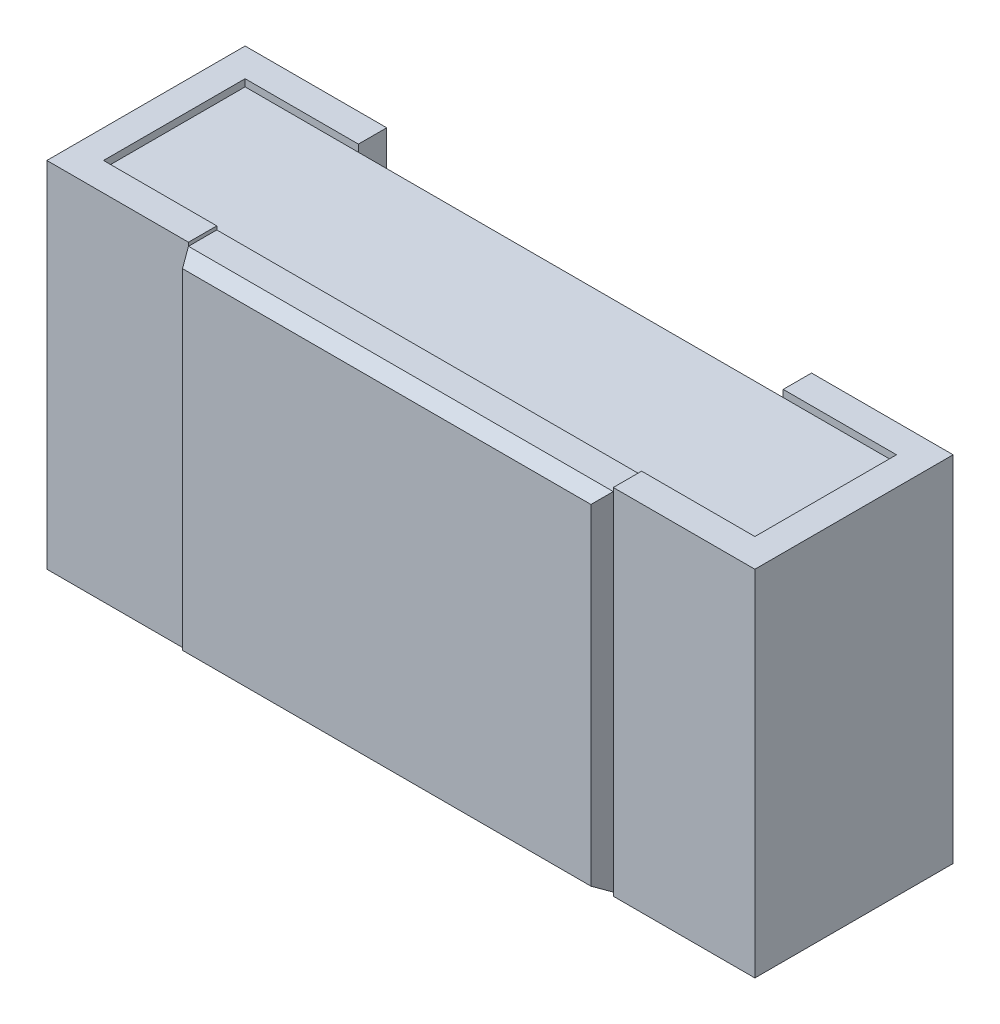
SolidWorks part; units mm, degrees
ref_plane "Спереди" through (0, 0, 0) normal (0, 0, 1) x (1, 0, 0)
ref_plane "Сверху" through (0, 0, 0) normal (0, 1, 0) x (1, 0, 0)
ref_plane "Справа" through (0, 0, 0) normal (1, 0, 0) x (0, 0, -1)
sketch "Эскиз2" plane through (0, 0, 0) normal (0, 0, 1) x (1, 0, 0)
  line L1 (-0.46, 0.24) -> (0.46, 0.24)
  line L2 (-0.46, 0.24) -> (-0.46, -0.24)
  line L3 (-0.46, -0.24) -> (0.46, -0.24)
  line L4 (0.46, 0.24) -> (0.46, -0.24)
  point P0 (0, 0)
extrude "Вытянуть2" add sketch "Эскиз2" along normal blind 0.2 from offset 0.04
sketch "Эскиз4" plane through (0, 0, 0) normal (0, 1, 0) x (1, 0, 0)
  line L0 (-0.5, 0) -> (-0.3, 0)
  line L1 (-0.46, -0.04) -> (-0.3, -0.04)
  line L2 (-0.5, 0) -> (-0.5, -0.28)
  line L3 (-0.3, 0) -> (-0.3, -0.04)
  line L4 (-0.46, -0.04) -> (-0.46, -0.24)
  line L5 (-0.5, -0.28) -> (-0.3, -0.28)
  line L6 (-0.3, -0.28) -> (-0.3, -0.24)
  line L7 (-0.3, -0.24) -> (-0.46, -0.24)
  line L8 (0, -0.3) -> (0, -0.2) construction
  line L9 (0.3, -0.24) -> (0.46, -0.24)
  line L10 (0.3, -0.28) -> (0.3, -0.24)
  line L11 (0.5, -0.28) -> (0.3, -0.28)
  line L12 (0.46, -0.04) -> (0.46, -0.24)
  line L13 (0.3, 0) -> (0.3, -0.04)
  line L14 (0.5, 0) -> (0.5, -0.28)
  line L15 (0.46, -0.04) -> (0.3, -0.04)
  line L16 (0.5, 0) -> (0.3, 0)
extrude "Вытянуть4" add sketch "Эскиз4" along normal blind 0.25 and the other way blind 0.25
sketch "Эскиз6" plane through (0, 0, 0) normal (0, 0, 1) x (1, 0, 0)
  line L1 (-0.3, 0.245) -> (0.3, 0.245)
  line L2 (-0.3, 0.245) -> (-0.3, -0.245)
  line L3 (-0.3, -0.245) -> (0.3, -0.245)
  line L4 (0.3, 0.245) -> (0.3, -0.245)
  point P0 (0, 0)
extrude "Вытянуть6" add sketch "Эскиз6" along normal blind 0.02 draft 30 and the other way blind 0.04 from offset 0.28
